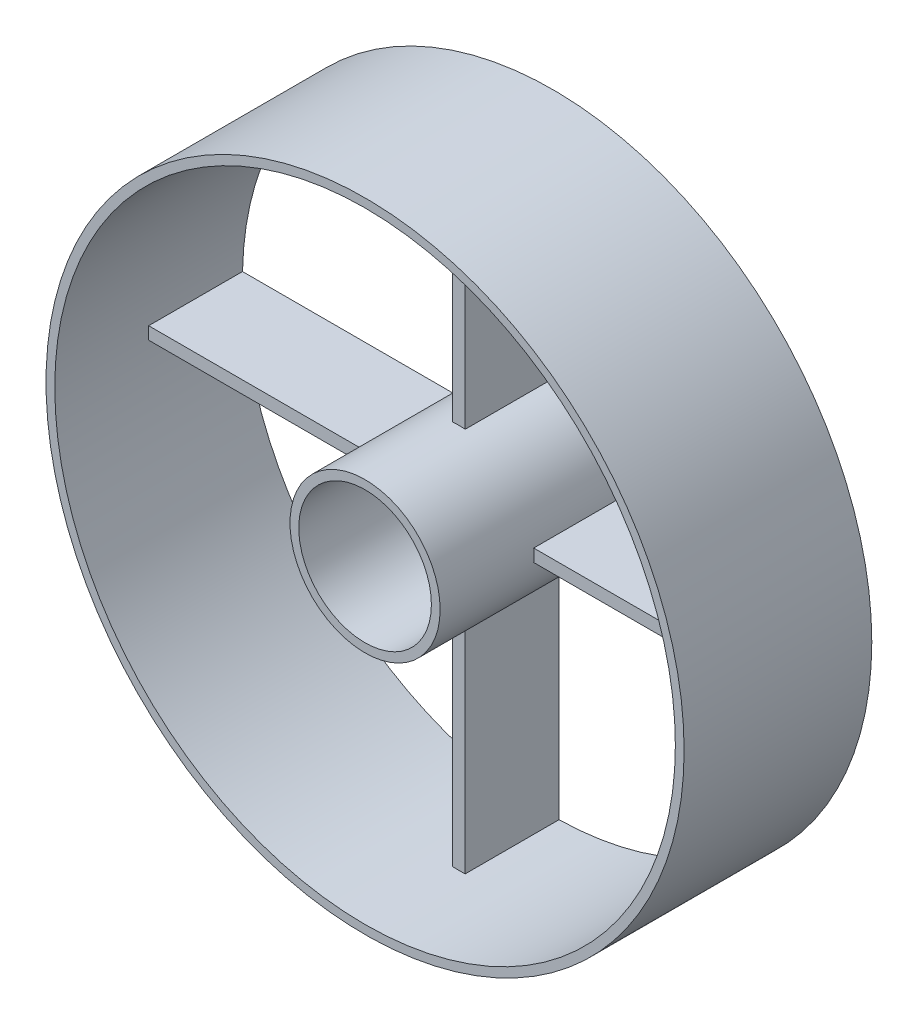
SolidWorks part; units mm, degrees
material "PVC Rigid"
ref_plane "Front Plane" through (0, 0, 0) normal (0, 0, 1) x (1, 0, 0)
ref_plane "Top Plane" through (0, 0, 0) normal (0, 1, 0) x (1, 0, 0)
ref_plane "Right Plane" through (0, 0, 0) normal (1, 0, 0) x (0, 0, -1)
sketch "Sketch1" plane through (0, 0, 0) normal (0, 0, 1) x (1, 0, 0)
  circle A0 centre (0, 0) radius 25.5
  circle A1 centre (0, 0) radius 6
  dimension "D1" = 51
  dimension "D2" = 12
extrude "Extrude-Thin1" add sketch "Sketch1" along normal blind 7.5 and the other way blind 7.5 thin thin type one direction reverse wall 0.7
sketch "Sketch2" plane through (0, 0, 0) normal (0, 0, 1) x (1, 0, 0)
  line L0 (-0.5, 24.795) -> (-0.5, 5.9791)
  line L1 (0.5, 24.795) -> (0.5, 5.9791)
  line L2 (-24.795, 0.5) -> (-5.9791, 0.5)
  line L3 (-24.795, -0.5) -> (-5.9791, -0.5)
  line L4 (-0.5, -24.795) -> (-0.5, -5.9791)
  line L5 (0.5, -24.795) -> (0.5, -5.9791)
  line L6 (5.9791, 0.5) -> (24.795, 0.5)
  line L7 (5.9791, -0.5) -> (24.795, -0.5)
  circle A0 centre (0, 0) radius 24.8 construction
  circle A1 centre (0, 0) radius 6 construction
  arc A2 (-5.9791, 0.5) -> (-5.9791, -0.5) centre (0, 0) ccw
  arc A3 (-0.5, -24.795) -> (0.5, -24.795) centre (0, 0) ccw
  arc A4 (5.9791, -0.5) -> (5.9791, 0.5) centre (0, 0) ccw
  arc A5 (0.5, 5.9791) -> (-0.5, 5.9791) centre (0, 0) ccw
  arc A6 (-0.5, -5.9791) -> (0.5, -5.9791) centre (0, 0) ccw
  arc A7 (-24.795, 0.5) -> (-24.795, -0.5) centre (0, 0) ccw
  arc A8 (0.5, 24.795) -> (-0.5, 24.795) centre (0, 0) ccw
  arc A9 (24.795, -0.5) -> (24.795, 0.5) centre (0, 0) ccw
  dimension "D1" = 1
  dimension "D2" = 1
  dimension "D3" = 0.5
  dimension "D4" = 0.5
extrude "Extrude1" add sketch "Sketch2" against normal blind 7.5
